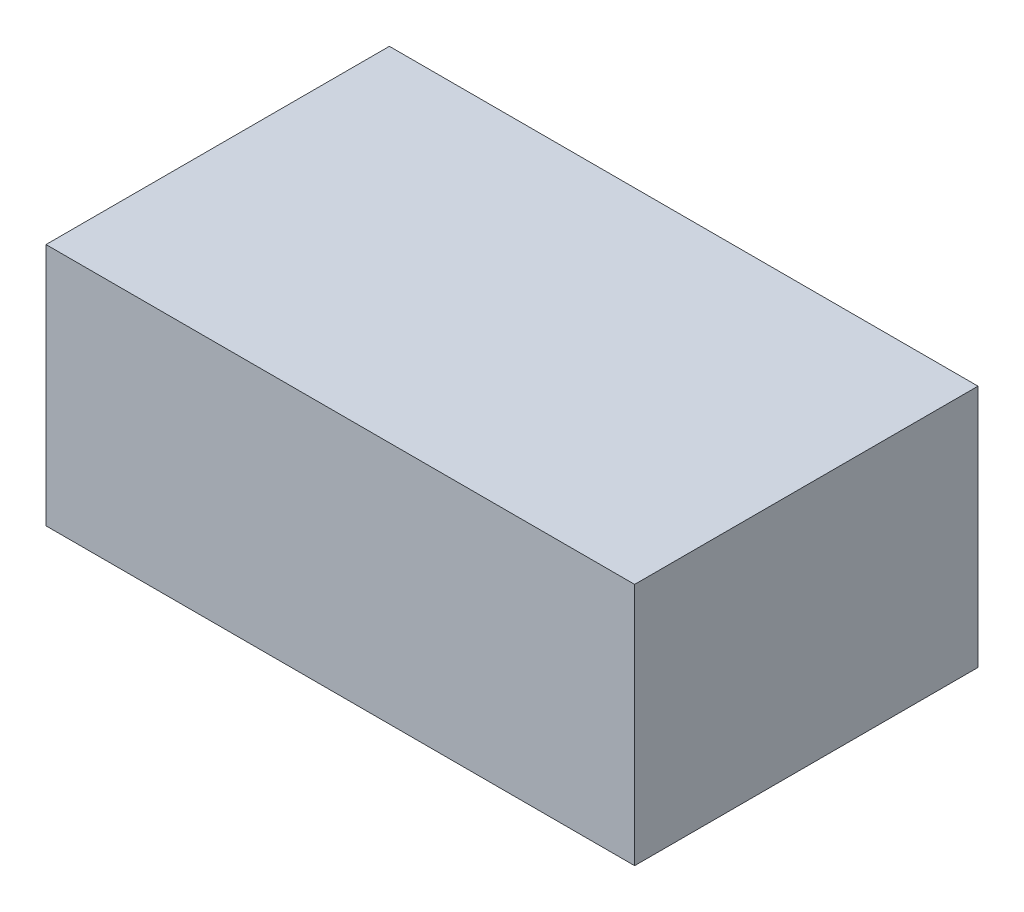
SolidWorks part; units mm, degrees
ref_plane "Front Plane" through (0, 0, 0) normal (0, 0, 1) x (1, 0, 0)
ref_plane "Top Plane" through (0, 0, 0) normal (0, 1, 0) x (1, 0, 0)
ref_plane "Right Plane" through (0, 0, 0) normal (1, 0, 0) x (0, 0, -1)
sketch "Sketch1" plane through (0, 0, 0) normal (0, 1, 0) x (1, 0, 0)
  line L1 (914.4, -533.4) -> (-914.4, -533.4)
  line L2 (914.4, -533.4) -> (914.4, 533.4)
  line L3 (914.4, 533.4) -> (-914.4, 533.4)
  line L4 (-914.4, -533.4) -> (-914.4, 533.4)
  line L5 (914.4, -533.4) -> (-914.4, 533.4) construction
  line L6 (914.4, 533.4) -> (-914.4, -533.4) construction
  point P0 (0, 0)
  dimension "D1" = 1066.8
  dimension "D2" = 1828.8
extrude "Boss-Extrude1" add sketch "Sketch1" along normal blind 756.92
